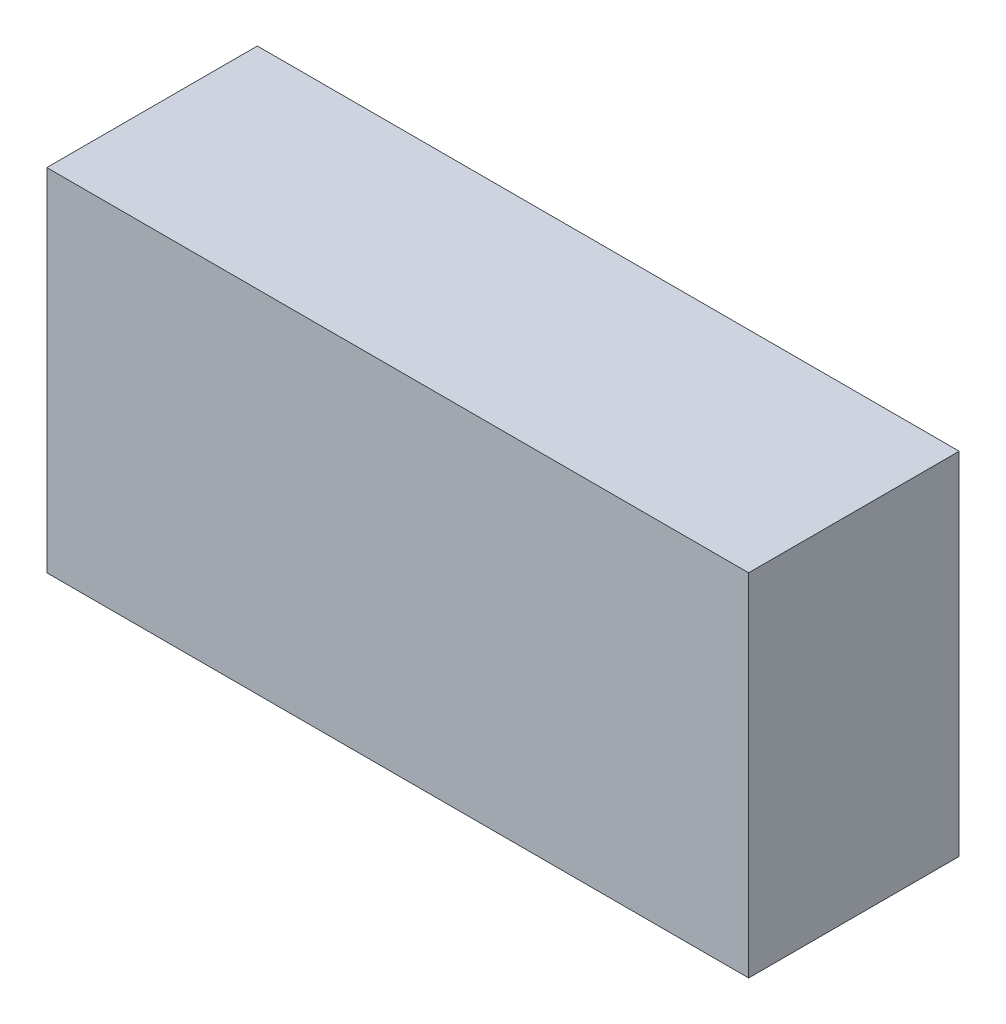
SolidWorks part; units mm, degrees
ref_plane "Front Plane" through (0, 0, 0) normal (0, 0, 1) x (1, 0, 0)
ref_plane "Top Plane" through (0, 0, 0) normal (0, 1, 0) x (1, 0, 0)
ref_plane "Right Plane" through (0, 0, 0) normal (1, 0, 0) x (0, 0, -1)
sketch "Sketch1" plane through (0, 0, 0) normal (0, 0, 1) x (1, 0, 0)
  line L1 (0, 0) -> (80, 0)
  line L2 (0, 0) -> (0, -40)
  line L3 (0, -40) -> (80, -40)
  line L4 (80, 0) -> (80, -40)
  dimension "D1" = 80
  dimension "D2" = 40
extrude "Boss-Extrude1" add sketch "Sketch1" along normal blind 24
